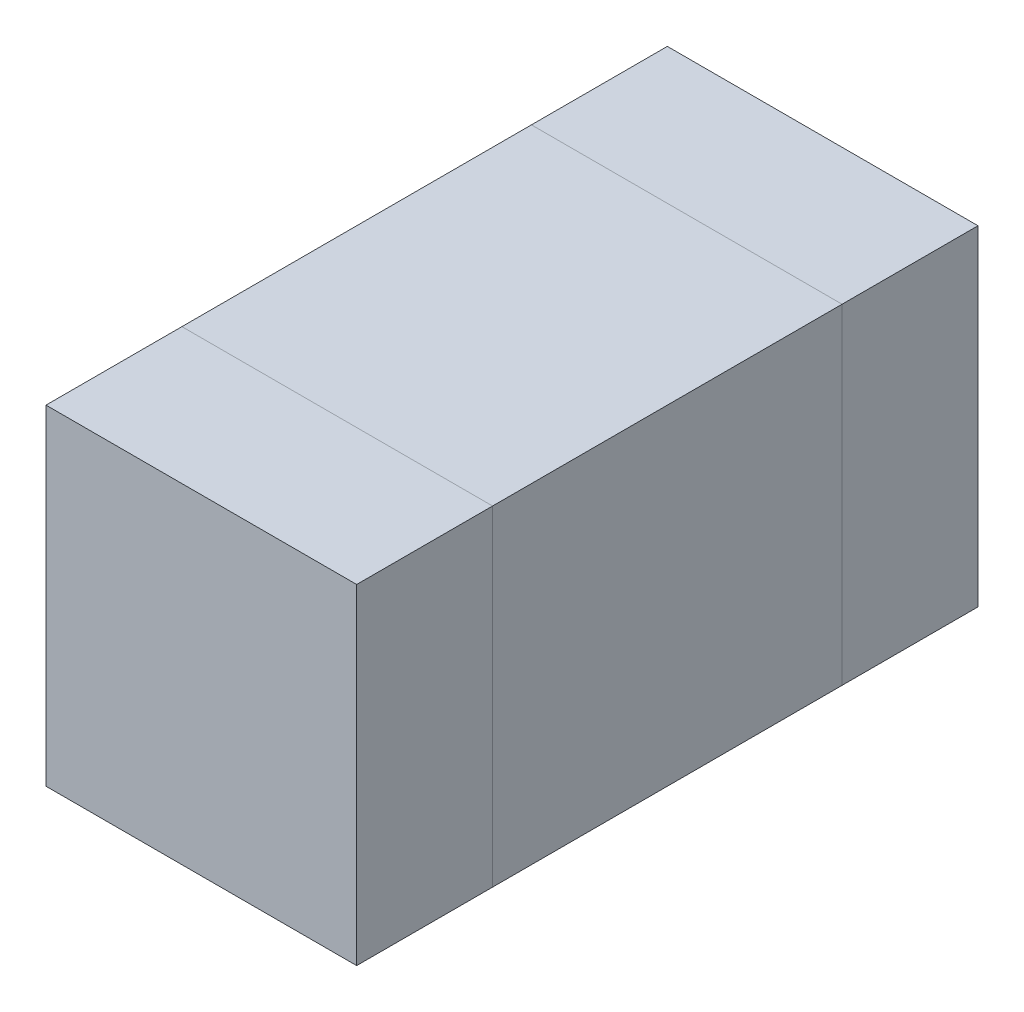
SolidWorks part; units mm, degrees
ref_plane "Front Plane" through (0, 0, 0) normal (0, 0, 1) x (1, 0, 0)
ref_plane "Top Plane" through (0, 0, 0) normal (0, 1, 0) x (1, 0, 0)
ref_plane "Right Plane" through (0, 0, 0) normal (1, 0, 0) x (0, 0, -1)
sketch "Sketch1" plane through (0, 0, 0) normal (0, 1, 0) x (1, 0, 0)
  line L1 (-0.8, 0.9) -> (0.8, 0.9)
  line L2 (-0.8, 0.9) -> (-0.8, -0.9)
  line L3 (-0.8, -0.9) -> (0.8, -0.9)
  line L4 (0.8, 0.9) -> (0.8, -0.9)
  line L5 (-0.8, 0.9) -> (0.8, -0.9) construction
  line L6 (-0.8, -0.9) -> (0.8, 0.9) construction
  point P0 (0, 0)
  dimension "D1" = 1.8
  dimension "D2" = 1.6
extrude "MB" add sketch "Sketch1" along normal blind 1.7
sketch "Sketch2" plane through (0, 0, 0.9) normal (0, 0, 1) x (1, 0, 0)
  line L4 (-0.8, 0) -> (0.8, 0)
  line L5 (0.8, 0) -> (0.8, 1.7)
  line L6 (0.8, 1.7) -> (-0.8, 1.7)
  line L7 (-0.8, 1.7) -> (-0.8, 0)
  line L8 (-0.8, 0) -> (0.8, 0)
  line L9 (0.8, 0) -> (0.8, 1.7)
  line L10 (0.8, 1.7) -> (-0.8, 1.7)
  line L11 (-0.8, 1.7) -> (-0.8, 0)
  dimension "D1" = 0
extrude "SB L" add sketch "Sketch2" along normal blind 0.7 separate body
sketch "Sketch3" plane through (0, 0, -0.9) normal (0, 0, -1) x (-1, 0, 0)
  line L4 (-0.8, 0) -> (0.8, 0)
  line L5 (0.8, 0) -> (0.8, 1.7)
  line L6 (0.8, 1.7) -> (-0.8, 1.7)
  line L7 (-0.8, 1.7) -> (-0.8, 0)
  line L8 (-0.8, 0) -> (0.8, 0)
  line L9 (0.8, 0) -> (0.8, 1.7)
  line L10 (0.8, 1.7) -> (-0.8, 1.7)
  line L11 (-0.8, 1.7) -> (-0.8, 0)
  dimension "D1" = 0
extrude "SB R" add sketch "Sketch3" along normal blind 0.7 separate body
